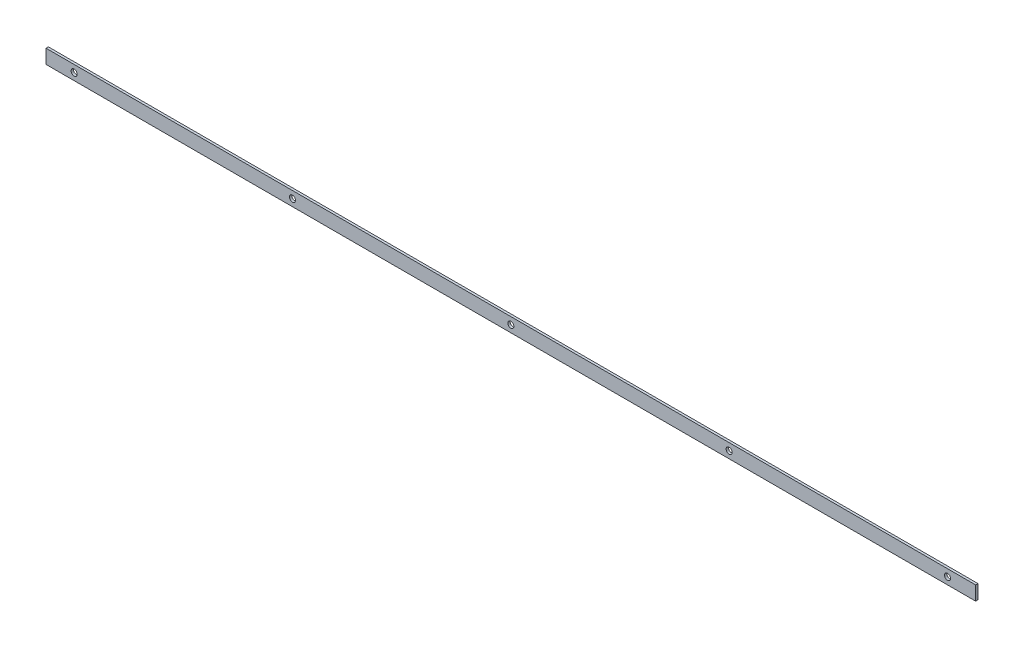
SolidWorks part; units mm, degrees
ref_plane "Plan de face" through (0, 0, 0) normal (0, 0, 1) x (1, 0, 0)
ref_plane "Plan de dessus" through (0, 0, 0) normal (0, 1, 0) x (1, 0, 0)
ref_plane "Plan de droite" through (0, 0, 0) normal (1, 0, 0) x (0, 0, -1)
sketch "Esquisse1" plane through (0, 0, 0) normal (0, 0, 1) x (1, 0, 0)
  line L0 (-991.5, 0) -> (991.5, 0)
other "Elément mécano-soudé1"
ref_plane "Plan1" through (-991.5, 0, 0) normal (1, 0, 0) x (0, 1, 0)
sketch "plat" plane through (-991.5, 0, 0) normal (1, 0, 0) x (0, 1, 0)
  line L0 (-15, 0) -> (15, 0) construction
  line L1 (-15, 2.5) -> (15, 2.5)
  line L2 (-15, 2.5) -> (-15, -2.5)
  line L3 (-15, -2.5) -> (15, -2.5)
  line L4 (15, 2.5) -> (15, -2.5)
  line L5 (0, 2.5) -> (0, -2.5) construction
  point P8 (0, 0)
  dimension "B" = 30
  dimension "A" = 5
sketch "Esquisse2" plane through (0, 0, -2.5) normal (0, 0, -1) x (-1, 0, 0)
  line L0 (991.5, 0) -> (-991.5, 0) construction
  line L1 (991.5, -15) -> (991.5, 15) construction
  line L2 (-991.5, -15) -> (-991.5, 15) construction
  point P0 (931.5, 0)
  point P5 (-931.5, 0)
ref_plane "Plan2" through (931.5, 0, 0) normal (1, 0, 0) x (0, 0, -1)
hole_wizard "Diamètre du perçage Ø13.0 (13)1" positions "Esquisse3" profile "Esquisse4" hole size "Ø13.0" standard "ISO" end condition through all
sketch "Esquisse3" plane through (0, 0, -2.5) normal (0, 0, -1) x (-1, 0, 0)
  point P0 (931.5, 0)
sketch "Esquisse4" plane through (-931.5, 0, -2.5) normal (1, 0, 0) x (0, 1, 0)
  line L0 (0, 0) -> (0, 5)
  line L1 (0, 5) -> (6.5, 5)
  line L2 (6.5, 5) -> (6.5, 0)
  line L5 (6.5, 0) -> (0, 0)
  line L11 (0, -6.35) -> (0, 107.95) construction
  dimension "Diamètre du perçage jusqu'au prochain" = 13
  dimension "Profondeur du perçage jusqu'au prochain" = 5
pattern_linear "Répétition linéaire2" count 5 spacing 465.75 along (1, 0, 0) of "Diamètre du perçage Ø13.0 (13)1"
equation "\"D2@Esquisse2\"=\"D1@Esquisse2\""
